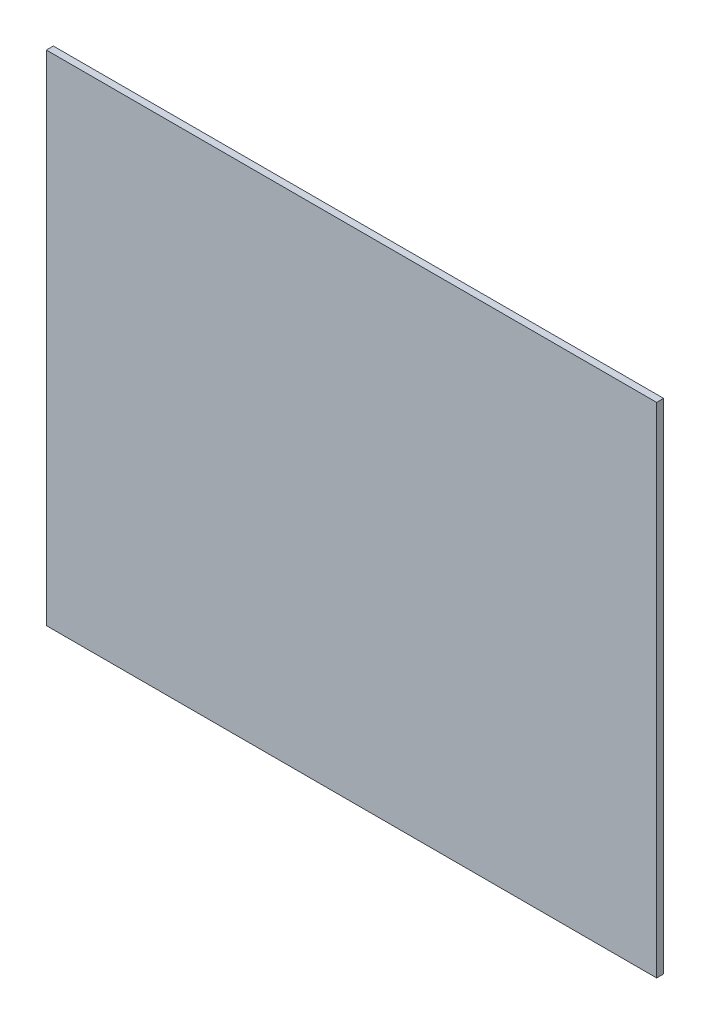
SolidWorks part; units mm, degrees
ref_plane "Alzado" through (0, 0, 0) normal (0, 0, 1) x (1, 0, 0)
ref_plane "Planta" through (0, 0, 0) normal (0, 1, 0) x (1, 0, 0)
ref_plane "Vista lateral" through (0, 0, 0) normal (1, 0, 0) x (0, 0, -1)
sketch "Croquis1" plane through (0, 0, 0) normal (0, 0, 1) x (1, 0, 0)
  line L1 (-55.0355, 36.5593) -> (75.9645, 36.5593)
  line L2 (-55.0355, 36.5593) -> (-55.0355, -70.4407)
  line L3 (-55.0355, -70.4407) -> (75.9645, -70.4407)
  line L4 (75.9645, 36.5593) -> (75.9645, -70.4407)
  dimension "D1" = 131
  dimension "D2" = 107
extrude "Saliente-Extruir1" add sketch "Croquis1" along normal blind 1.5
